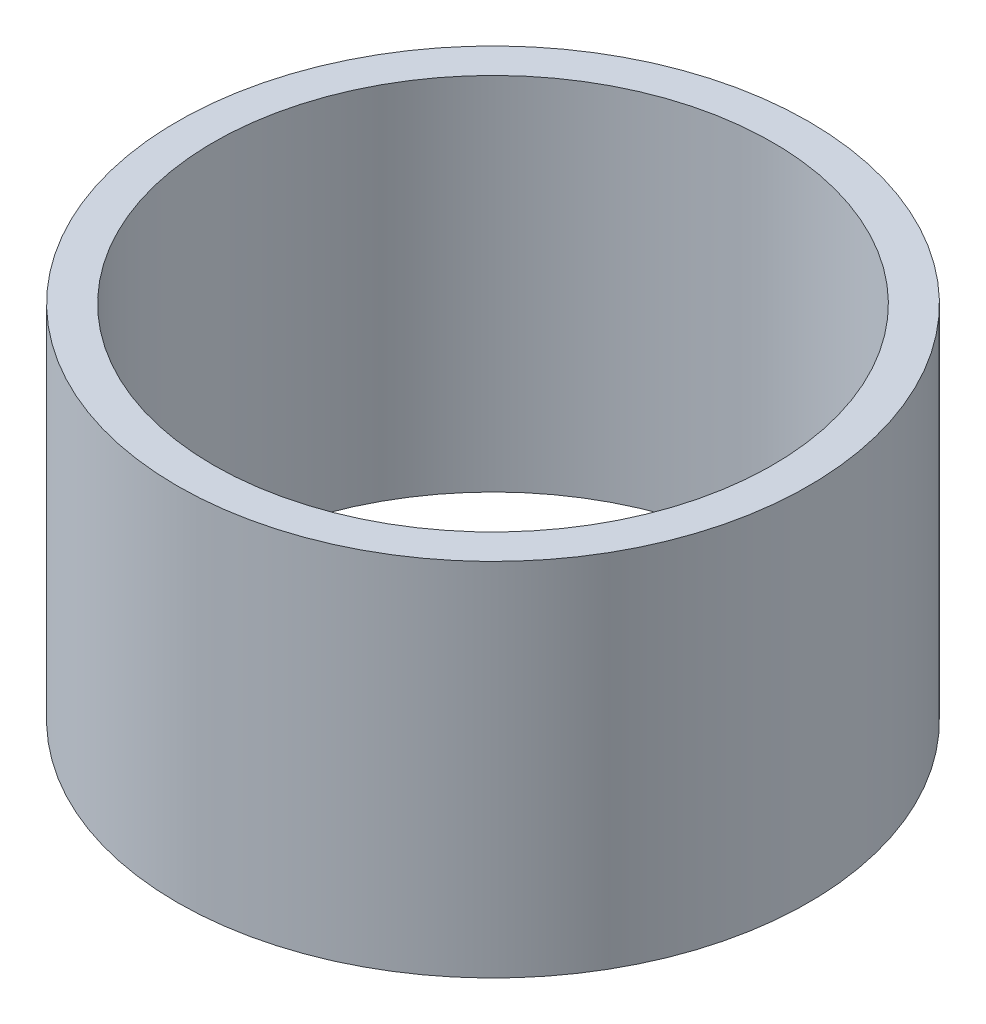
SolidWorks part; units mm, degrees
material "Epoxy, Unfilled"
ref_plane "Front Plane" through (0, 0, 0) normal (0, 0, 1) x (1, 0, 0)
ref_plane "Top Plane" through (0, 0, 0) normal (0, 1, 0) x (1, 0, 0)
ref_plane "Right Plane" through (0, 0, 0) normal (1, 0, 0) x (0, 0, -1)
sketch "Sketch1" plane through (0, 0, 0) normal (0, 1, 0) x (1, 0, 0)
  circle A0 centre (0, 0) radius 55.5625
  circle A1 centre (0, 0) radius 55.5625
  circle A2 centre (0, 0) radius 49.2125
extrude "Boss-Extrude1" add sketch "Sketch1" along normal blind 63.5 contours A0 A2
